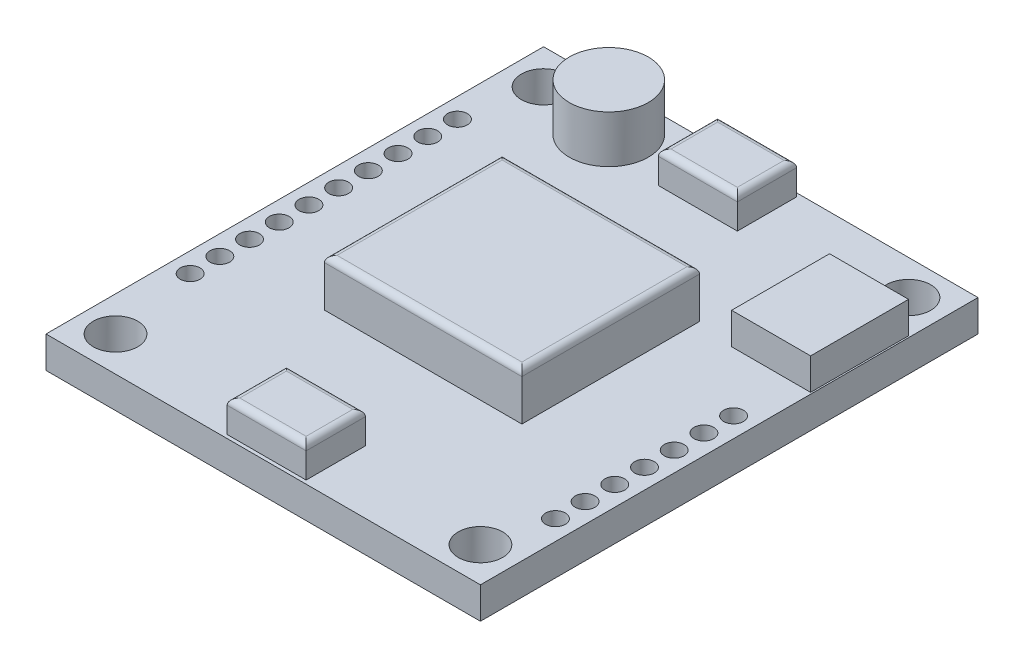
SolidWorks part; units mm, degrees
ref_plane "Front Plane" through (0, 0, 0) normal (0, 0, 1) x (1, 0, 0)
ref_plane "Top Plane" through (0, 0, 0) normal (0, 1, 0) x (1, 0, 0)
ref_plane "Right Plane" through (0, 0, 0) normal (1, 0, 0) x (0, 0, -1)
sketch "Sketch1" plane through (0, 0, 0) normal (0, 1, 0) x (1, 0, 0)
  line L1 (17.4625, 20) -> (-17.4625, 20)
  line L2 (17.4625, 20) -> (17.4625, -20)
  line L3 (17.4625, -20) -> (-17.4625, -20)
  line L4 (-17.4625, 20) -> (-17.4625, -20)
  line L5 (17.4625, 20) -> (-17.4625, -20) construction
  line L6 (17.4625, -20) -> (-17.4625, 20) construction
  point P0 (0, 0)
  dimension "D1" = 40
  dimension "D2" = 34.925
extrude "Boss-Extrude1" add sketch "Sketch1" along normal blind 2.54 contours L1 L4 L3 L2
ref_plane "Plane1" through (0, 0, 0) normal (-1, 0, 0) x (0, 0, 1)
ref_plane "Plane2" through (0, 0, 0) normal (0, 0, -1) x (-1, 0, 0)
hole_wizard "9/64 (0.14063) Diameter Hole1" positions "Sketch2" profile "Sketch3" hole size "9/64" standard "ANSI Inch" end condition up to next
sketch "Sketch2" plane through (0, 2.54, 0) normal (0, 1, 0) x (1, 0, 0)
  line L0 (-17.4625, 20) -> (-17.4625, -20) construction
  line L1 (17.4625, 20) -> (-17.4625, 20) construction
  line L2 (0, 1.397) -> (0, -1.397) construction
  line L3 (1.397, 0) -> (-1.397, 0) construction
  point P0 (-14.6685, 17.206)
  point P19 (14.6685, 17.206)
  point P22 (14.6685, -17.206)
  point P23 (-14.6685, -17.206)
  dimension "D1" = 2.794
  dimension "D2" = 2.794
sketch "Sketch3" plane through (-14.6685, 2.54, -17.206) normal (1, 0, 0) x (0, 0, 1)
  line L0 (0, 0) -> (0, 2.54)
  line L1 (0, 2.54) -> (1.786, 2.54)
  line L2 (1.786, 2.54) -> (1.786, 0)
  line L5 (1.786, 0) -> (0, 0)
  line L11 (0, -6.35) -> (0, 107.95) construction
  dimension "Thru Hole Dia." = 3.572
  dimension "Thru Hole Depth" = 2.54
hole_wizard "1/16 (0.0625) Diameter Hole1" positions "Sketch4" profile "Sketch5" hole size "1/16" standard "ANSI Inch" end condition up to next
sketch "Sketch4" plane through (0, 2.54, 0) normal (0, 1, 0) x (1, 0, 0)
  line L2 (-17.4625, 20) -> (-17.4625, -20) construction
  line L3 (17.4625, -20) -> (-17.4625, -20) construction
  line L4 (0, 1.397) -> (0, -1.397) construction
  point P0 (-15.875, -10)
  point P23 (-15.875, -7.6124)
  point P24 (-15.875, -5.2248)
  point P25 (-15.875, -2.8372)
  point P26 (-15.875, -0.4496)
  point P27 (-15.875, 1.938)
  point P28 (-15.875, 4.3256)
  point P29 (-15.875, 6.7132)
  point P30 (-15.875, 9.1008)
  point P31 (-15.875, 11.4884)
  point P34 (15.875, 1.938)
  point P35 (15.875, -0.4496)
  point P36 (15.875, -2.8372)
  point P37 (15.875, -5.2248)
  point P38 (15.875, -7.6124)
  point P39 (15.875, -10)
  point P40 (15.875, -12.3812)
  dimension "D1" = 1.5875
  dimension "D2" = 10
  dimension "D4" = 2.3813
  dimension "D3" = 10
sketch "Sketch5" plane through (-15.875, 2.54, 10) normal (1, 0, 0) x (0, 0, 1)
  line L0 (0, 0) -> (0, 2.54)
  line L1 (0, 2.54) -> (0.7937, 2.54)
  line L2 (0.7937, 2.54) -> (0.7937, 0)
  line L5 (0.7937, 0) -> (0, 0)
  line L11 (0, -6.35) -> (0, 107.95) construction
  dimension "Thru Hole Dia." = 1.5875
  dimension "Thru Hole Depth" = 2.54
sketch "Sketch6" plane through (0, 2.54, 0) normal (0, 1, 0) x (1, 0, 0)
  line L0 (-17.4625, 20) -> (-17.4625, -20) construction
  line L2 (17.4625, -20) -> (-17.4625, -20) construction
  circle A0 centre (-8.7312, 16.5125) radius 3.175
  dimension "D1" = 6.35
  dimension "D2" = 8.7312
  dimension "D3" = 36.5125
extrude "Boss-Extrude2" add sketch "Sketch6" along normal blind 3.81
sketch "Sketch7" plane through (0, 2.54, 0) normal (0, 1, 0) x (1, 0, 0)
  line L1 (-7.9375, -7.1437) -> (7.9375, -7.1437)
  line L2 (-7.9375, -7.1437) -> (-7.9375, 7.1437)
  line L3 (-7.9375, 7.1437) -> (7.9375, 7.1437)
  line L4 (7.9375, -7.1437) -> (7.9375, 7.1437)
  line L5 (-7.9375, -7.1437) -> (7.9375, 7.1437) construction
  line L6 (-7.9375, 7.1437) -> (7.9375, -7.1437) construction
  point P0 (0, 0)
  dimension "D1" = 14.2875
  dimension "D2" = 15.875
extrude "Boss-Extrude3" add sketch "Sketch7" along normal blind 3.81
fillet "Fillet1" radius 0.508 4 edges at (7.9375, 6.35, 0) (0, 6.35, -7.1437) (0, 6.35, 7.1437) (-7.9375, 6.35, 0)
sketch "Sketch8" plane through (0, 2.54, 0) normal (0, 1, 0) x (1, 0, 0)
  line L6 (17.4625, -20) -> (-17.4625, -20) construction
  line L7 (10.9855, 6.67) -> (17.3355, 6.67)
  line L8 (10.9855, 6.67) -> (10.9855, 14.544)
  line L9 (10.9855, 14.544) -> (17.3355, 14.544)
  line L10 (17.3355, 6.67) -> (17.3355, 14.544)
  line L11 (10.9855, 6.67) -> (17.3355, 14.544) construction
  line L12 (10.9855, 14.544) -> (17.3355, 6.67) construction
  line L13 (17.4625, 20) -> (17.4625, -20) construction
  point P0 (14.1605, 10.607)
  dimension "D1" = 6.35
  dimension "D2" = 7.874
  dimension "D3" = 26.67
  dimension "D4" = 0.127
extrude "Boss-Extrude4" add sketch "Sketch8" along normal blind 2.54
sketch "Sketch10" plane through (0, 2.54, 0) normal (0, 1, 0) x (1, 0, 0)
  line L0 (17.4625, 20) -> (-17.4625, 20) construction
  line L1 (3.1649, 19.7143) -> (-3.1851, 19.7143)
  line L2 (3.1649, 19.7143) -> (3.1649, 14.9518)
  line L3 (3.1649, 14.9518) -> (-3.1851, 14.9518)
  line L4 (-3.1851, 19.7143) -> (-3.1851, 14.9518)
  line L5 (3.1649, 19.7143) -> (-3.1851, 14.9518) construction
  line L6 (3.1649, 14.9518) -> (-3.1851, 19.7143) construction
  line L7 (1.397, 0) -> (-1.397, 0) construction
  line L8 (3.1649, -14.9518) -> (-3.1851, -14.9518)
  line L9 (-3.1851, -19.7143) -> (-3.1851, -14.9518)
  line L10 (3.1649, -19.7143) -> (-3.1851, -19.7143)
  line L11 (3.1649, -19.7143) -> (3.1649, -14.9518)
  point P0 (-0.0101, 17.333)
  dimension "D1" = 6.35
  dimension "D2" = 4.7625
  dimension "D3" = 2.667
extrude "Boss-Extrude5" add sketch "Sketch10" along normal blind 2.54
fillet "Fillet2" radius 0.508 8 edges at (3.1649, 5.08, 17.333) (-0.0101, 5.08, 14.9518) (-3.1851, 5.08, 17.333) (-0.0101, 5.08, 19.7143) (3.1649, 5.08, -17.333) (-0.0101, 5.08, -19.7143) (-0.0101, 5.08, -14.9518) (-3.1851, 5.08, -17.333)
